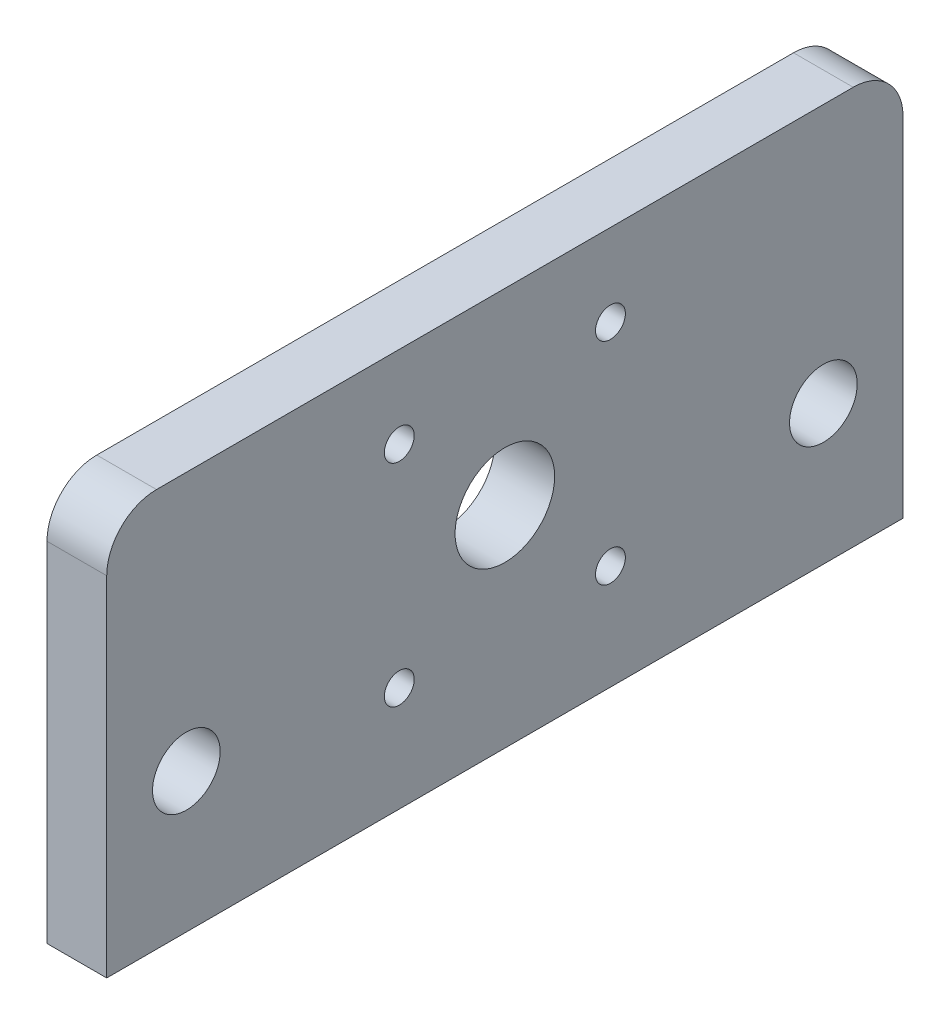
SolidWorks part; units mm, degrees
ref_plane "Front Plane" through (0, 0, 0) normal (0, 0, 1) x (1, 0, 0)
ref_plane "Top Plane" through (0, 0, 0) normal (0, 1, 0) x (1, 0, 0)
ref_plane "Right Plane" through (0, 0, 0) normal (1, 0, 0) x (0, 0, -1)
sketch "Sketch3" plane through (0, 0, 0) normal (1, 0, 0) x (0, 0, -1)
  line L1 (-40, 20) -> (40, 20)
  line L2 (-40, 20) -> (-40, -20)
  line L3 (-40, -20) -> (40, -20)
  line L4 (40, 20) -> (40, -20)
  line L5 (-40, 20) -> (40, -20) construction
  line L6 (-40, -20) -> (40, 20) construction
  point P0 (0, 0)
  dimension "D1" = 80
  dimension "D2" = 40
extrude "Boss-Extrude3" add sketch "Sketch3" against normal blind 6
sketch "Sketch4" plane through (0, 0, 0) normal (1, 0, 0) x (0, 0, -1)
  line L0 (0, 10.6052) -> (0, -44.0587) construction
  line L1 (0, 1.15) -> (-21.2132, 22.3632) construction
  line L2 (55.8256, 1.15) -> (11.727, 1.15) construction
  line L3 (-40, -20) -> (40, -20) construction
  line L4 (-40, 20) -> (-40, -20) construction
  line L5 (40, -20) -> (40, 20) construction
  circle A0 centre (0, 1.15) radius 5
  circle A1 centre (-10.6066, 11.7566) radius 1.5
  circle A2 centre (10.6066, 11.7566) radius 1.5
  circle A3 centre (10.6066, -9.4566) radius 1.5
  circle A4 centre (-10.6066, -9.4566) radius 1.5
  circle A6 centre (32, -6) radius 3.4
  circle A7 centre (-32, -6) radius 3.4
  circle A8 centre (0, 1.15) radius 17.95 construction
  dimension "D1" = 10
  dimension "D2" = 3
  dimension "D4" = 45
  dimension "D5" = 35.9
  dimension "D6" = 6.8
  dimension "D8" = 6.8
  dimension "D3" = 15
  dimension "D7" = 14
  dimension "D9" = 14
  dimension "D10" = 8
  dimension "D11" = 8
  dimension "D12" = 21.15
  dimension "D13" = 40
extrude "Cut-Extrude1" cut sketch "Sketch4" against normal blind 8
fillet "Fillet1" radius 5 2 edges at (-3, 20, -40) (-3, 20, 40)
